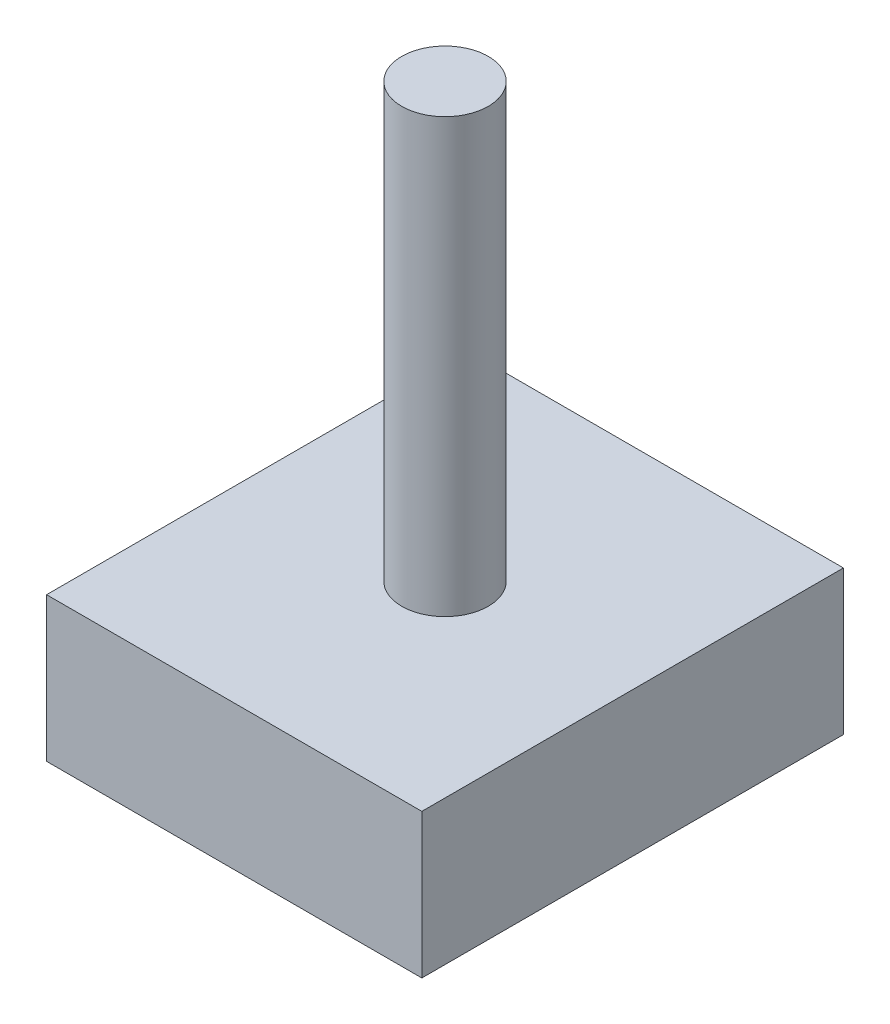
SolidWorks part; units mm, degrees
ref_plane "前视基准面" through (0, 0, 0) normal (0, 0, 1) x (1, 0, 0)
ref_plane "上视基准面" through (0, 0, 0) normal (0, 1, 0) x (1, 0, 0)
ref_plane "右视基准面" through (0, 0, 0) normal (1, 0, 0) x (0, 0, -1)
other "Configuration Table"
sketch "草图1" plane through (0, 0, 0) normal (0, 1, 0) x (1, 0, 0)
  line L1 (-6.5, 7.3025) -> (6.5, 7.3025)
  line L2 (-6.5, 7.3025) -> (-6.5, -7.3025)
  line L3 (-6.5, -7.3025) -> (6.5, -7.3025)
  line L4 (6.5, 7.3025) -> (6.5, -7.3025)
  line L5 (-6.5, 7.3025) -> (6.5, -7.3025) construction
  line L6 (-6.5, -7.3025) -> (6.5, 7.3025) construction
  point P0 (0, 0)
  dimension "D1" = 13
extrude "凸台-拉伸1" add sketch "草图1" along normal blind 5
sketch "草图2" plane through (0, 5, 0) normal (0, 1, 0) x (1, 0, 0)
  circle A0 centre (0, 0) radius 1.5
extrude "凸台-拉伸2" add sketch "草图2" along normal blind 15
